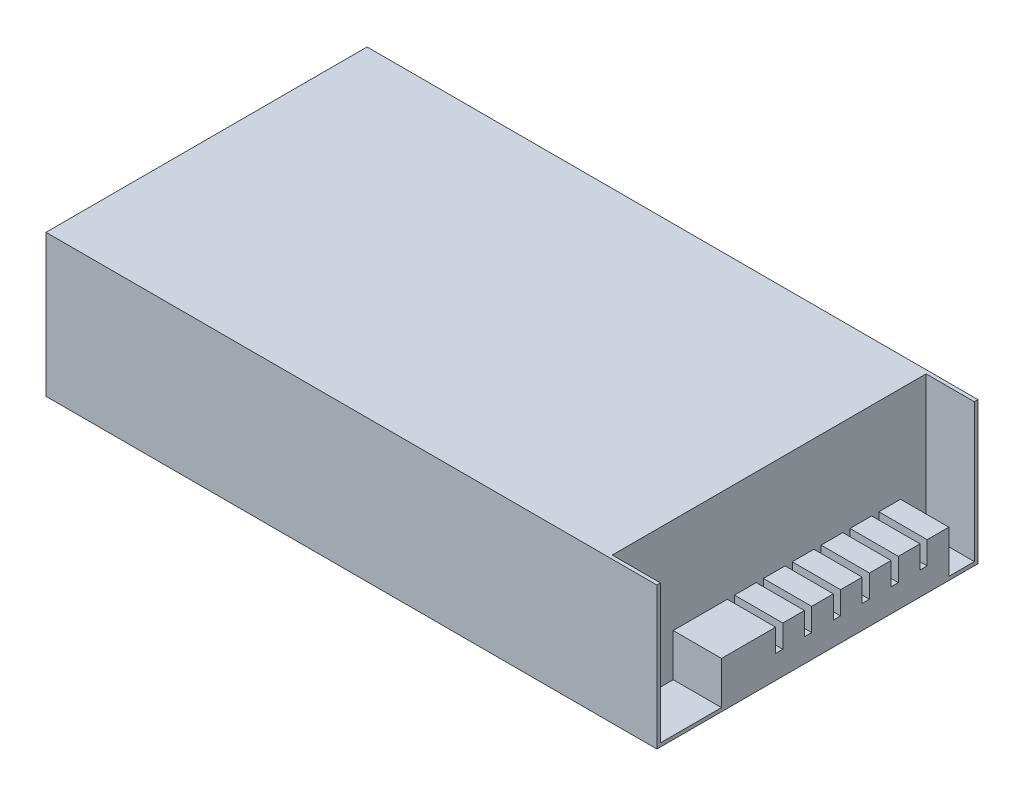
SolidWorks part; units mm, degrees
ref_plane "Front Plane" through (0, 0, 0) normal (0, 0, 1) x (1, 0, 0)
ref_plane "Top Plane" through (0, 0, 0) normal (0, 1, 0) x (1, 0, 0)
ref_plane "Right Plane" through (0, 0, 0) normal (1, 0, 0) x (0, 0, -1)
sketch "Sketch1" plane through (0, 0, 0) normal (0, 1, 0) x (1, 0, 0)
  line L1 (0, 0) -> (215, 0)
  line L2 (0, 0) -> (0, 113)
  line L3 (0, 113) -> (215, 113)
  line L4 (215, 0) -> (215, 113)
  dimension "D1" = 113
  dimension "D2" = 215
extrude "Boss-Extrude1" add sketch "Sketch1" along normal blind 50
sketch "Sketch2" plane through (215, 0, 0) normal (1, 0, 0) x (0, 0, -1)
  line L0 (0, 0) -> (113, 0) construction
  line L1 (1.27, 50) -> (111.73, 50)
  line L2 (1.27, 50) -> (1.27, 1.27)
  line L3 (1.27, 1.27) -> (111.73, 1.27)
  line L4 (111.73, 50) -> (111.73, 1.27)
  line L5 (1.27, 50) -> (111.73, 1.27) construction
  line L6 (1.27, 1.27) -> (111.73, 50) construction
  line L7 (113, 50) -> (113, 0) construction
  line L8 (0, 50) -> (0, 0) construction
  line L9 (0, 50) -> (113, 50) construction
  point P4 (56.5, 25.635)
  point P12 (1.27, 50)
  dimension "D1" = 1.27
  dimension "D2" = 1.27
  dimension "D3" = 1.27
extrude "Cut-Extrude1" cut sketch "Sketch2" against normal blind 17 contours L3 L4 L1 L2
sketch "Sketch3" plane through (0, 0, 0) normal (-1, 0, 0) x (0, 0, 1)
  line L4 (-1.27, 1.27) -> (-1.27, 50)
  line L5 (-111.73, 1.27) -> (-1.27, 1.27)
  line L6 (-111.73, 50) -> (-111.73, 1.27)
  line L7 (-1.27, 50) -> (-111.73, 50)
  line L8 (-1.27, 1.27) -> (-1.27, 50)
  line L9 (-111.73, 1.27) -> (-1.27, 1.27)
  line L10 (-111.73, 50) -> (-111.73, 1.27)
  line L11 (-1.27, 50) -> (-111.73, 50)
  dimension "D1" = 0
extrude "Cut-Extrude2" [suppressed] cut sketch "Sketch3" against normal blind 2.921
sketch "Sketch4" plane through (0, 1.27, 0) normal (0, 1, 0) x (1, 0, 0)
  line L0 (215, 1.27) -> (215, 111.73) construction
  line L1 (215, 22.73) -> (198, 22.73)
  line L2 (215, 22.73) -> (215, 102.73)
  line L3 (215, 102.73) -> (198, 102.73)
  line L4 (198, 22.73) -> (198, 102.73)
  line L5 (215, 22.73) -> (198, 102.73) construction
  line L6 (215, 102.73) -> (198, 22.73) construction
  line L7 (198, 1.27) -> (198, 111.73) construction
  line L9 (198, 111.73) -> (215, 111.73) construction
  point P4 (206.5, 62.73)
  dimension "D1" = 80
  dimension "D2" = 9
extrude "Boss-Extrude2" add sketch "Sketch4" along normal blind 15
sketch "Sketch5" [suppressed] plane through (0, 1.27, 0) normal (0, 1, 0) x (1, 0, 0)
  line L0 (0, 8.255) -> (0, 5.08)
  line L1 (0, 111.73) -> (0, 0) construction
  line L2 (0, 5.08) -> (4.0005, 5.08)
  line L3 (4.0005, 8.255) -> (0, 8.255)
  line L4 (215, 104.237) -> (215, 107.412)
  line L5 (215, 80.264) -> (215, 111.73) construction
  line L6 (215, 107.412) -> (210.9995, 107.412)
  line L7 (210.9995, 104.237) -> (215, 104.237)
  line L8 (215, 113) -> (0, 113) construction
  line L9 (2.921, 0) -> (0, 0) construction
  arc A0 (4.0005, 5.08) -> (4.0005, 8.255) centre (4.0005, 6.6675) ccw
  arc A1 (210.9995, 107.412) -> (210.9995, 104.237) centre (210.9995, 105.8245) ccw
  dimension "D2" = 5.588
  dimension "D1" = 3.175
  dimension "D3" = 5.588
  dimension "D4" = 5.08
extrude "Cut-Extrude3" [suppressed] cut sketch "Sketch5" against normal blind 22.352
sketch "Sketch6" plane through (0, 0, 0) normal (0, -1, 0) x (1, 0, 0)
  line L1 (215, 0) -> (215, -113) construction
  line L2 (0, 0) -> (215, 0) construction
  circle A0 centre (113.146, -65.278) radius 1.27
  circle A1 centre (190.87, -65.278) radius 1.27
  dimension "D1" = 80.264
  dimension "D2" = 64.008
  dimension "D3" = 22.86
  dimension "D4" = 2.54
extrude "Cut-Extrude4" cut sketch "Sketch6" against normal blind 10.16
sketch "Sketch7" plane through (0, 16.27, 0) normal (0, 1, 0) x (1, 0, 0)
  line L0 (198, 102.73) -> (198, 22.73) construction
  line L1 (215, 102.73) -> (198, 102.73)
  line L2 (215, 102.73) -> (215, 95.11)
  line L3 (215, 95.11) -> (198, 95.11)
  line L4 (198, 102.73) -> (198, 95.11)
  line L5 (206.5, 95.11) -> (206.5, 102.73) construction
  line L6 (215, 98.92) -> (198, 98.92) construction
  line L7 (206.5, 84.95) -> (206.5, 92.57) construction
  line L8 (215, 88.76) -> (198, 88.76) construction
  line L9 (215, 92.57) -> (215, 84.95)
  line L10 (215, 92.57) -> (198, 92.57)
  line L11 (198, 92.57) -> (198, 84.95)
  line L12 (215, 84.95) -> (198, 84.95)
  line L13 (206.5, 74.79) -> (206.5, 82.41) construction
  line L14 (215, 78.6) -> (198, 78.6) construction
  line L15 (215, 82.41) -> (215, 74.79)
  line L16 (215, 82.41) -> (198, 82.41)
  line L17 (198, 82.41) -> (198, 74.79)
  line L18 (215, 74.79) -> (198, 74.79)
  line L19 (206.5, 64.63) -> (206.5, 72.25) construction
  line L20 (215, 68.44) -> (198, 68.44) construction
  line L21 (215, 72.25) -> (215, 64.63)
  line L22 (215, 72.25) -> (198, 72.25)
  line L23 (198, 72.25) -> (198, 64.63)
  line L24 (215, 64.63) -> (198, 64.63)
  line L25 (206.5, 54.47) -> (206.5, 62.09) construction
  line L26 (215, 58.28) -> (198, 58.28) construction
  line L27 (215, 62.09) -> (215, 54.47)
  line L28 (215, 62.09) -> (198, 62.09)
  line L29 (198, 62.09) -> (198, 54.47)
  line L30 (215, 54.47) -> (198, 54.47)
  line L31 (206.5, 44.31) -> (206.5, 51.93) construction
  line L32 (215, 48.12) -> (198, 48.12) construction
  line L33 (215, 51.93) -> (215, 44.31)
  line L34 (215, 51.93) -> (198, 51.93)
  line L35 (198, 51.93) -> (198, 44.31)
  line L36 (215, 44.31) -> (198, 44.31)
  line L37 (206.5, 34.15) -> (206.5, 41.77) construction
  line L38 (215, 37.96) -> (198, 37.96) construction
  line L39 (215, 41.77) -> (215, 34.15)
  line L40 (215, 41.77) -> (198, 41.77)
  line L41 (198, 41.77) -> (198, 34.15)
  line L42 (215, 34.15) -> (198, 34.15)
  line L43 (206.5, 98.92) -> (206.5, 88.76) construction
  line L44 (215, 34.15) -> (215, 95.11)
  line L45 (198, 95.11) -> (198, 34.15)
  point P15 (206.5, 88.76)
  point P24 (206.5, 78.6)
  point P33 (206.5, 68.44)
  point P42 (206.5, 58.28)
  point P51 (206.5, 48.12)
  point P60 (206.5, 37.96)
  point P104 (206.5, 98.92)
  line M51 (215, 22.73) -> (215, 102.73)
  line M53 (198, 102.73) -> (198, 22.73)
  dimension "D2" = 10.16
  dimension "D3" = 7.62
  dimension "D1" = 7
extrude "Cut-Extrude5" cut sketch "Sketch7" against normal blind 8 contours L10 L3 M51 M53 | L16 L12 M51 M53 | L22 L18 M51 M53 | L28 L24 M51 M53 | L34 L30 M51 M53 | L40 L36 M51 M53
